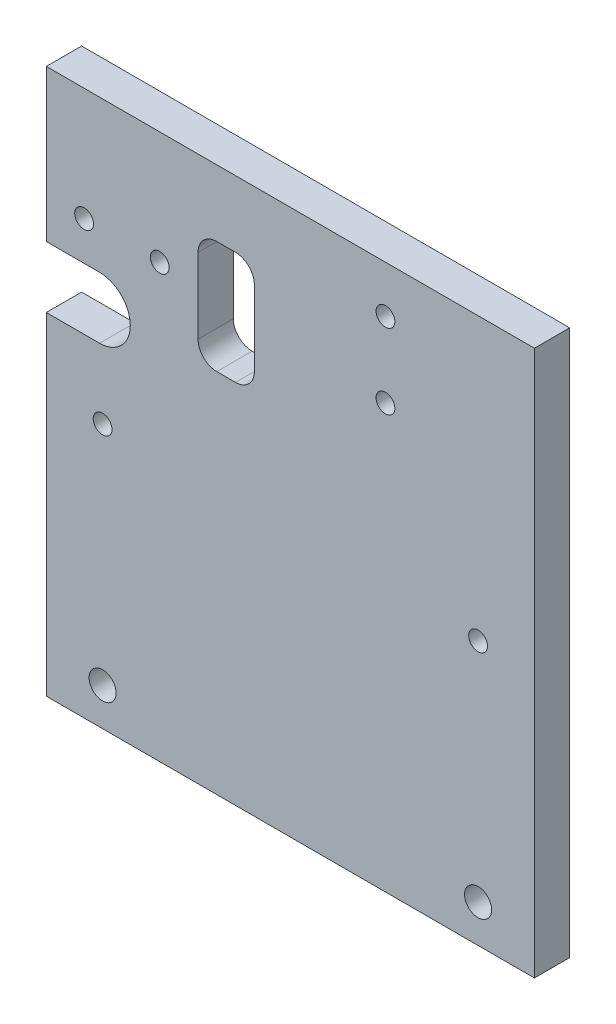
SolidWorks part; units mm, degrees
ref_plane "Front Plane" through (0, 0, 0) normal (0, 0, 1) x (1, 0, 0)
ref_plane "Top Plane" through (0, 0, 0) normal (0, 1, 0) x (1, 0, 0)
ref_plane "Right Plane" through (0, 0, 0) normal (1, 0, 0) x (0, 0, -1)
sketch "Sketch1" plane through (0, 0, 0) normal (0, 0, 1) x (1, 0, 0)
  line L5 (0, 0) -> (100, 0) construction
  line L6 (0, 0) -> (0, 60.26) construction
  line L7 (0, 60.26) -> (100, 60.26) construction
  line L8 (100, 0) -> (100, 60.26) construction
  line L9 (0, 0) -> (100, 60.26) construction
  line L10 (0, 60.26) -> (100, 0) construction
  line L11 (-15, -10) -> (115, -10)
  line L12 (-15, -10) -> (-15, 135.26)
  line L13 (-15, 135.26) -> (115, 135.26)
  line L14 (115, -10) -> (115, 135.26)
  line L15 (-15, -10) -> (115, 135.26) construction
  line L16 (-15, 135.26) -> (115, -10) construction
  circle A0 centre (0, 0) radius 3.6
  circle A1 centre (0, 60.26) radius 2.5
  circle A2 centre (100, 60.26) radius 2.5
  circle A3 centre (100, 0) radius 3.6
  point P6 (50, 30.13)
  point P16 (50, 62.63)
  dimension "D1" = 7.2
  dimension "D3" = 5
  dimension "D2" = 60.26
  dimension "D4" = 100
  dimension "D5" = 15
  dimension "D6" = 15
  dimension "D7" = 10
  dimension "D8" = 75
extrude "Boss-Extrude1" add sketch "Sketch1" along normal blind 9.4
sketch "Sketch2" plane through (0, 0, 9.4) normal (0, 0, 1) x (1, 0, 0)
  circle A2 centre (75.33, 122.7664) radius 2.5
  circle A3 centre (75.33, 102.7664) radius 2.5
  dimension "D1" = 5
  dimension "D2" = 5
extrude "Cut-Extrude1" cut sketch "Sketch2" against normal through all
sketch "Sketch3" plane through (0, 0, 0) normal (0, 0, -1) x (-1, 0, 0)
  line L1 (-35.4075, 117.5704) -> (-30.4075, 117.5704)
  line L2 (-40.4075, 112.5704) -> (-40.4075, 92.5704)
  line L3 (-35.4075, 87.5704) -> (-30.4075, 87.5704)
  line L4 (-25.4075, 112.5704) -> (-25.4075, 92.5704)
  line L5 (-40.4075, 117.5704) -> (-25.4075, 87.5704) construction
  line L6 (-40.4075, 87.5704) -> (-25.4075, 117.5704) construction
  arc A0 (-25.4075, 92.5704) -> (-30.4075, 87.5704) centre (-30.4075, 92.5704) cw
  arc A1 (-35.4075, 87.5704) -> (-40.4075, 92.5704) centre (-35.4075, 92.5704) cw
  arc A2 (-40.4075, 112.5704) -> (-35.4075, 117.5704) centre (-35.4075, 112.5704) cw
  arc A3 (-30.4075, 117.5704) -> (-25.4075, 112.5704) centre (-30.4075, 112.5704) cw
  point P4 (-32.9075, 102.5704)
  dimension "D1" = 5
  dimension "D2" = 30
  dimension "D3" = 15
extrude "Cut-Extrude2" cut sketch "Sketch3" against normal through all
sketch "Sketch4" plane through (0, 0, 9.4) normal (0, 0, 1) x (1, 0, 0)
  line L1 (-15, 135.26) -> (-15, -10) construction
  line L4 (-15, 78.5) -> (-15, 94.86)
  line L5 (-15, 94.86) -> (-0.81, 94.86)
  line L6 (-15, 78.5) -> (-0.81, 78.5)
  line L8 (115, 135.26) -> (-15, 135.26) construction
  arc A2 (-0.81, 94.86) -> (-0.81, 78.5) centre (-0.81, 86.68) cw
  dimension "D1" = 14.19
  dimension "D2" = 16.36
  dimension "D3" = 40.4
extrude "Cut-Extrude3" cut sketch "Sketch4" against normal through all
sketch "Sketch5" plane through (0, 0, 9.4) normal (0, 0, 1) x (1, 0, 0)
  circle A0 centre (-4.9269, 105.186) radius 2.5
  circle A1 centre (15.2153, 105.186) radius 2.5
extrude "Cut-Extrude4" cut sketch "Sketch5" against normal through all
